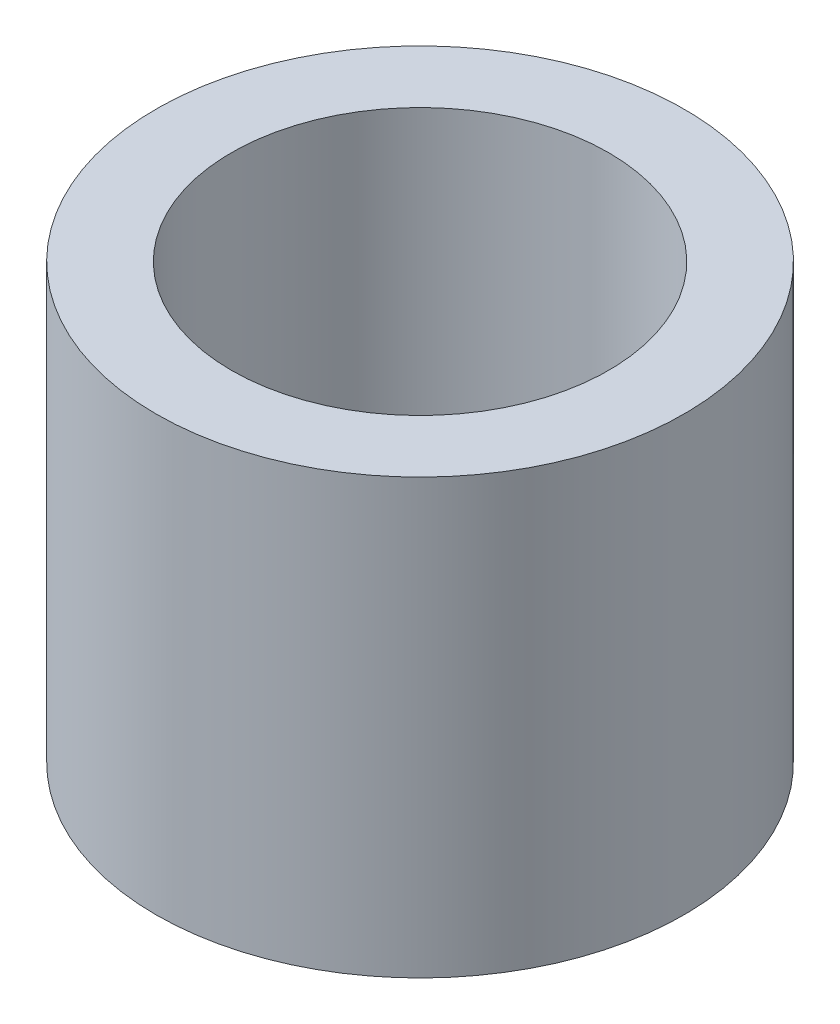
SolidWorks part; units mm, degrees
material "Fireplace Stuff"
ref_plane "Front Plane" through (0, 0, 0) normal (0, 0, 1) x (1, 0, 0)
ref_plane "Top Plane" through (0, 0, 0) normal (0, 1, 0) x (1, 0, 0)
ref_plane "Right Plane" through (0, 0, 0) normal (1, 0, 0) x (0, 0, -1)
sketch "Sketch3" plane through (0, 0, 0) normal (0, 1, 0) x (1, 0, 0)
  circle A0 centre (0, 0) radius 44.45
  circle A2 centre (0, 0) radius 31.75
  dimension "D1" = 88.9
  dimension "D2" = 12.7
extrude "Boss-Extrude1" add sketch "Sketch3" along normal blind 73.025
